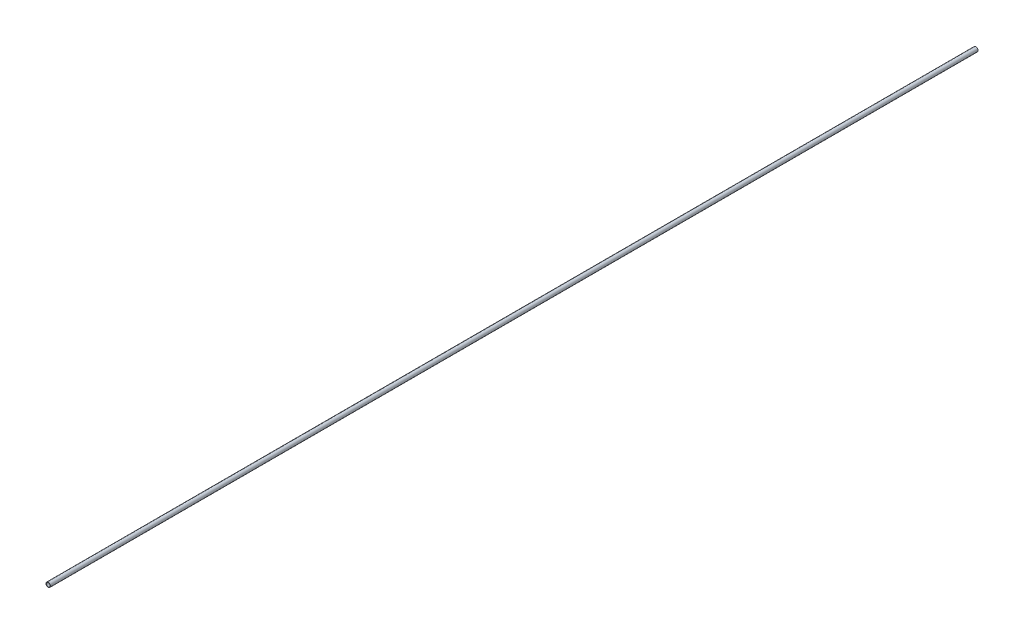
SolidWorks part; units mm, degrees
material "A-Glass Fiber"
ref_plane "Front Plane" through (0, 0, 0) normal (0, 0, 1) x (1, 0, 0)
ref_plane "Top Plane" through (0, 0, 0) normal (0, 1, 0) x (1, 0, 0)
ref_plane "Right Plane" through (0, 0, 0) normal (1, 0, 0) x (0, 0, -1)
sketch "Sketch1" plane through (0, 0, 0) normal (0, 0, 1) x (1, 0, 0)
  circle A0 centre (0, 0) radius 2.5
  dimension "D1" = 5
extrude "Extrude-Thin1" add sketch "Sketch1" along normal mid plane 1046 thin thin type one direction reverse wall 0.5
